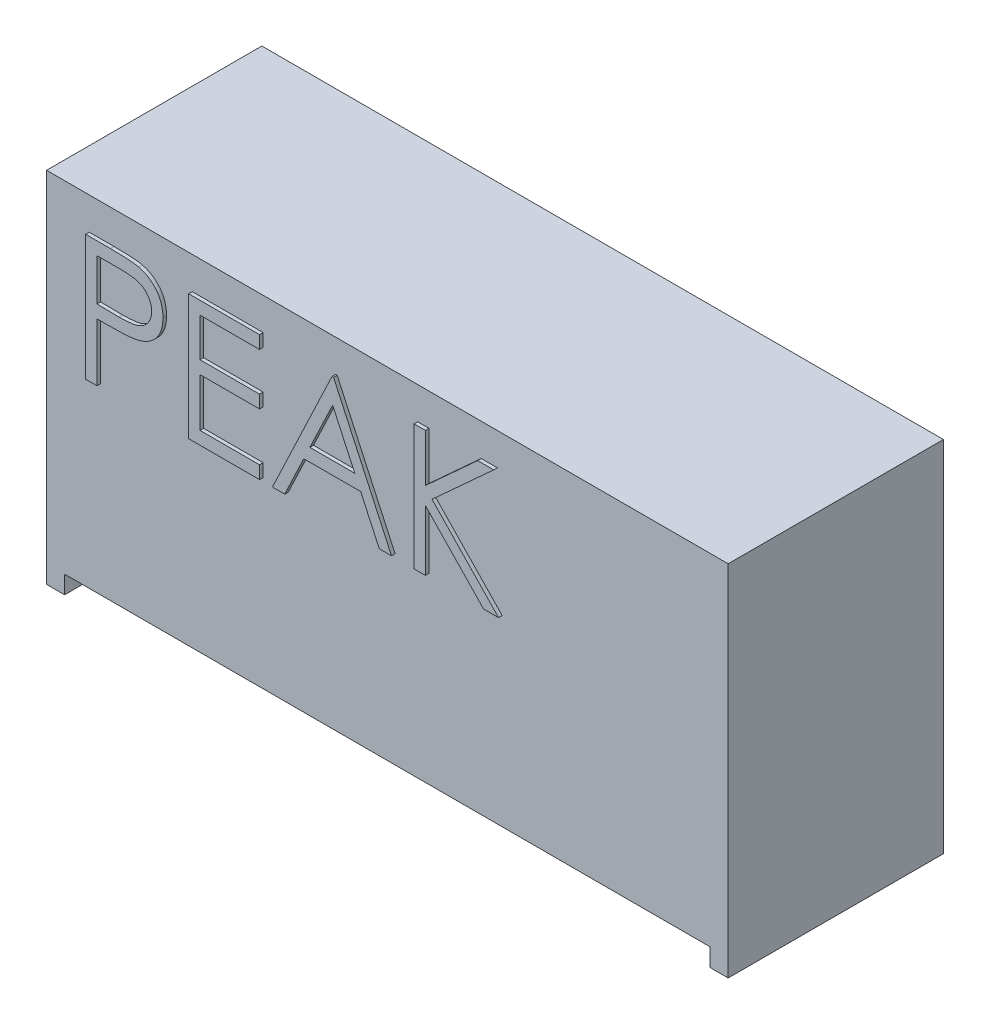
SolidWorks part; units mm, degrees
ref_plane "Спереди" through (0, 0, 0) normal (0, 0, 1) x (1, 0, 0)
ref_plane "Сверху" through (0, 0, 0) normal (0, 1, 0) x (1, 0, 0)
ref_plane "Справа" through (0, 0, 0) normal (1, 0, 0) x (0, 0, -1)
sketch "Эскиз1" plane through (0, 0, 0) normal (0, 0, 1) x (1, 0, 0)
  line L0 (-9, -5) -> (-9, -4.5)
  line L1 (-9.5, 5) -> (9.5, 5)
  line L2 (-9.5, 5) -> (-9.5, -5)
  line L3 (-9.5, -5) -> (-9, -5)
  line L4 (9.5, 5) -> (9.5, -5)
  line L5 (-9.5, 5) -> (9.5, -5) construction
  line L6 (-9.5, -5) -> (9.5, 5) construction
  line L7 (-9, -4.5) -> (9, -4.5)
  line L8 (9, -4.5) -> (9, -5)
  line L9 (9, -5) -> (9.5, -5)
  point P0 (0, 0)
  point P8 (-9, -4.5)
  point P11 (9, -4.5)
  dimension "D1" = 19
  dimension "D2" = 10
  dimension "D3" = 0.5
  dimension "D4" = 0.5
  dimension "D5" = 0.5
extrude "Бобышка-Вытянуть1" add sketch "Эскиз1" along normal blind 6
sketch "Эскиз2" plane through (0, 0, 6) normal (0, 0, 1) x (1, 0, 0)
  text T0 "PEAK" font "Century Gothic" height 3.5
  point P1 (-8.7176, 0.5791)
  point P2 (-8.759, 0.5998)
  point P3 (0, 0)
extrude "Бобышка-Вытянуть2" add sketch "Эскиз2" along normal blind 0.1 separate body
